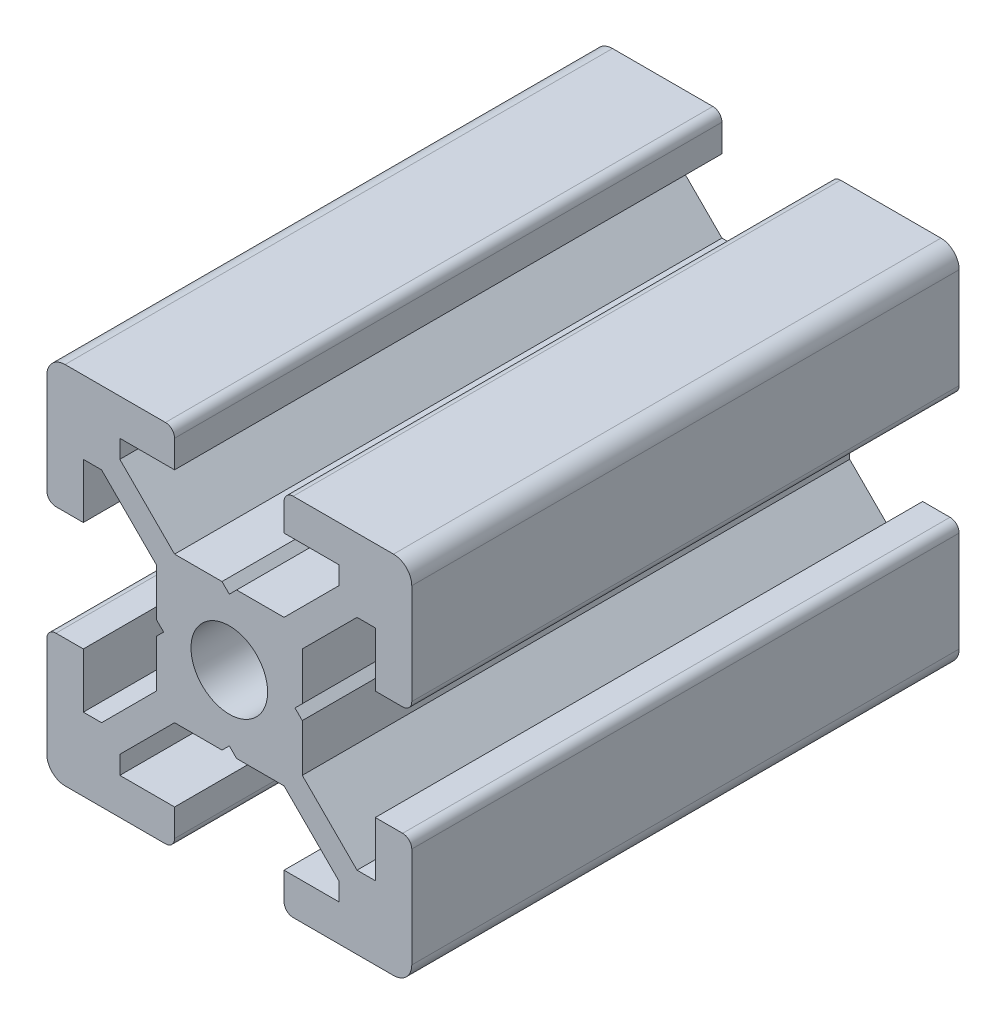
SolidWorks part; units mm, degrees
material "Lega 6061"
ref_plane "Piano frontale" through (0, 0, 0) normal (0, 0, 1) x (1, 0, 0)
ref_plane "Piano superiore" through (0, 0, 0) normal (0, 1, 0) x (1, 0, 0)
ref_plane "Piano destro" through (0, 0, 0) normal (1, 0, 0) x (0, 0, -1)
sketch "Schizzo1" plane through (0, 0, 0) normal (0, 0, 1) x (1, 0, 0)
  line L0 (0, 0) -> (-10, 0) construction
  line L1 (0, 0) -> (0, 10) construction
  line L2 (-3.6, 0) -> (-4, 0.4)
  line L3 (-4, 0.4) -> (-4, 3)
  line L4 (-4, 3) -> (-7, 6)
  line L5 (-7, 6) -> (-8, 6)
  line L6 (-8, 6) -> (-8, 3)
  line L7 (-8, 3) -> (-9.5, 3)
  line L8 (-10, 3.5) -> (-10, 9)
  line L9 (0, 0) -> (-10, 10) construction
  line L10 (0, 3.6) -> (-0.4, 4)
  line L11 (-0.4, 4) -> (-3, 4)
  line L12 (-3, 4) -> (-6, 7)
  line L13 (-6, 7) -> (-6, 8)
  line L14 (-6, 8) -> (-3, 8)
  line L15 (-3, 8) -> (-3, 9.5)
  line L16 (-3.5, 10) -> (-9, 10)
  line L17 (0, 0) -> (-10, -10) construction
  line L18 (-3.5, -10) -> (-9, -10)
  line L19 (-3, -8) -> (-3, -9.5)
  line L20 (-6, -8) -> (-3, -8)
  line L21 (-6, -7) -> (-6, -8)
  line L22 (-3, -4) -> (-6, -7)
  line L23 (-0.4, -4) -> (-3, -4)
  line L24 (0, -3.6) -> (-0.4, -4)
  line L25 (-10, -3.5) -> (-10, -9)
  line L26 (-8, -3) -> (-9.5, -3)
  line L27 (-8, -6) -> (-8, -3)
  line L28 (-7, -6) -> (-8, -6)
  line L29 (-4, -3) -> (-7, -6)
  line L30 (-4, -0.4) -> (-4, -3)
  line L31 (-3.6, 0) -> (-4, -0.4)
  line L32 (0, 0) -> (10, -10) construction
  line L33 (0, 0) -> (10, 10) construction
  line L34 (3.6, 0) -> (4, -0.4)
  line L35 (4, -0.4) -> (4, -3)
  line L36 (4, -3) -> (7, -6)
  line L37 (7, -6) -> (8, -6)
  line L38 (8, -6) -> (8, -3)
  line L39 (8, -3) -> (9.5, -3)
  line L40 (10, -3.5) -> (10, -9)
  line L41 (0, -3.6) -> (0.4, -4)
  line L42 (0.4, -4) -> (3, -4)
  line L43 (3, -4) -> (6, -7)
  line L44 (6, -7) -> (6, -8)
  line L45 (6, -8) -> (3, -8)
  line L46 (3, -8) -> (3, -9.5)
  line L47 (3.5, -10) -> (9, -10)
  line L48 (3.5, 10) -> (9, 10)
  line L49 (3, 8) -> (3, 9.5)
  line L50 (6, 8) -> (3, 8)
  line L51 (6, 7) -> (6, 8)
  line L52 (3, 4) -> (6, 7)
  line L53 (0.4, 4) -> (3, 4)
  line L54 (0, 3.6) -> (0.4, 4)
  line L55 (10, 3.5) -> (10, 9)
  line L56 (8, 3) -> (9.5, 3)
  line L57 (8, 6) -> (8, 3)
  line L58 (7, 6) -> (8, 6)
  line L59 (4, 3) -> (7, 6)
  line L60 (4, 0.4) -> (4, 3)
  line L61 (3.6, 0) -> (4, 0.4)
  arc A0 (-10, 9) -> (-9, 10) centre (-9, 9) cw
  arc A1 (-3, 9.5) -> (-3.5, 10) centre (-3.5, 9.5) ccw
  arc A2 (-9.5, 3) -> (-10, 3.5) centre (-9.5, 3.5) cw
  arc A3 (-9.5, -3) -> (-10, -3.5) centre (-9.5, -3.5) ccw
  arc A4 (-3, -9.5) -> (-3.5, -10) centre (-3.5, -9.5) cw
  arc A5 (-10, -9) -> (-9, -10) centre (-9, -9) ccw
  arc A6 (10, -9) -> (9, -10) centre (9, -9) cw
  arc A7 (3, -9.5) -> (3.5, -10) centre (3.5, -9.5) ccw
  arc A8 (9.5, -3) -> (10, -3.5) centre (9.5, -3.5) cw
  arc A9 (9.5, 3) -> (10, 3.5) centre (9.5, 3.5) ccw
  arc A10 (3, 9.5) -> (3.5, 10) centre (3.5, 9.5) cw
  arc A11 (10, 9) -> (9, 10) centre (9, 9) ccw
  circle A12 centre (0, 0) radius 2.1
  point P24 (-3, 10)
  point P27 (-10, 3)
  point P49 (-10, -3)
  point P50 (-3, -10)
  point P92 (3, -10)
  point P93 (10, -3)
  point P94 (10, 3)
  point P95 (3, 10)
  dimension "D2" = 1
  dimension "D12" = 0.5
  dimension "D13" = 4.2
  dimension "D3" = 8
  dimension "D4" = 0.4
  dimension "D5" = 45
  dimension "D6" = 6
  dimension "D7" = 12
  dimension "D8" = 20
  dimension "D9" = 2
  dimension "D10" = 4
  dimension "D11" = 45
extrude "Estrusione-Estrusione1" add sketch "Schizzo1" along normal blind 30
